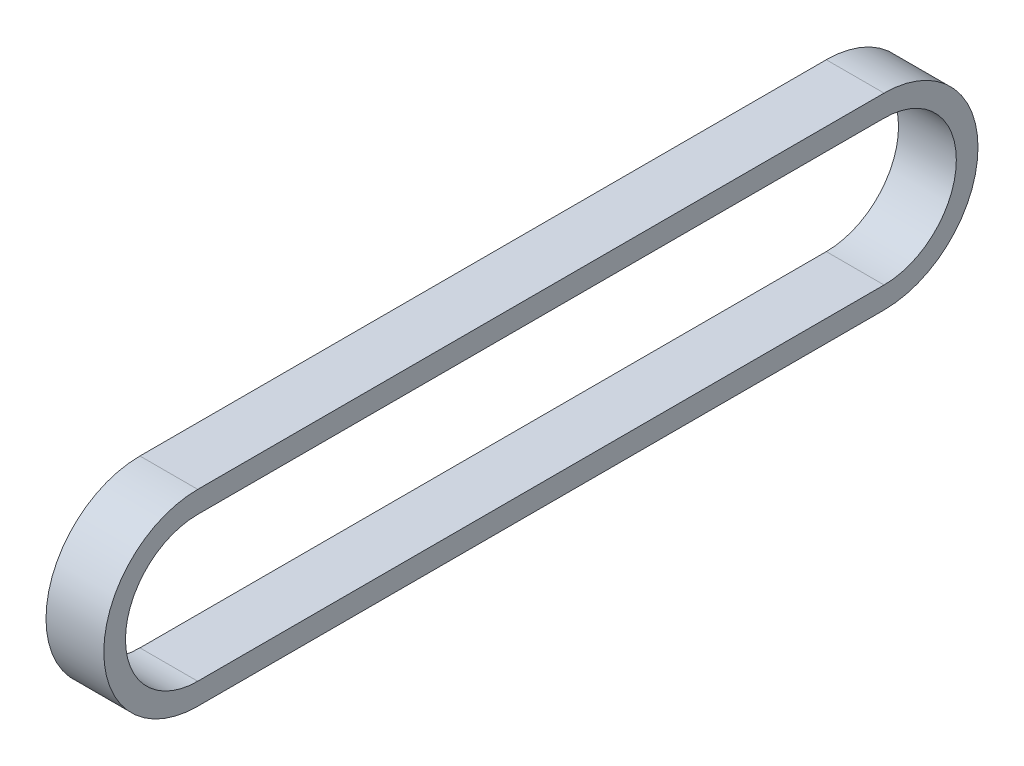
SolidWorks part; units mm, degrees
ref_plane "前视基准面" through (0, 0, 0) normal (0, 0, 1) x (1, 0, 0)
ref_plane "上视基准面" through (0, 0, 0) normal (0, 1, 0) x (1, 0, 0)
ref_plane "右视基准面" through (0, 0, 0) normal (1, 0, 0) x (0, 0, -1)
other "Configuration Table"
sketch "草图1" plane through (0, 0, 0) normal (1, 0, 0) x (0, 0, -1)
  line L0 (0, 0) -> (95, 0)
  line L1 (0, 20) -> (95, 20)
  line L2 (0, 23) -> (95, 23)
  line L3 (0, -3) -> (95, -3)
  arc A0 (0, 0) -> (0, 20) centre (0, 10) cw
  arc A1 (95, 20) -> (95, 0) centre (95, 10) cw
  arc A2 (95, 23) -> (95, -3) centre (95, 10) cw
  arc A3 (0, -3) -> (0, 23) centre (0, 10) cw
  dimension "D2" = 10
  dimension "D3" = 10
  dimension "D1" = 95
  dimension "D4" = 3
extrude "凸台-拉伸1" add sketch "草图1" along normal blind 8
